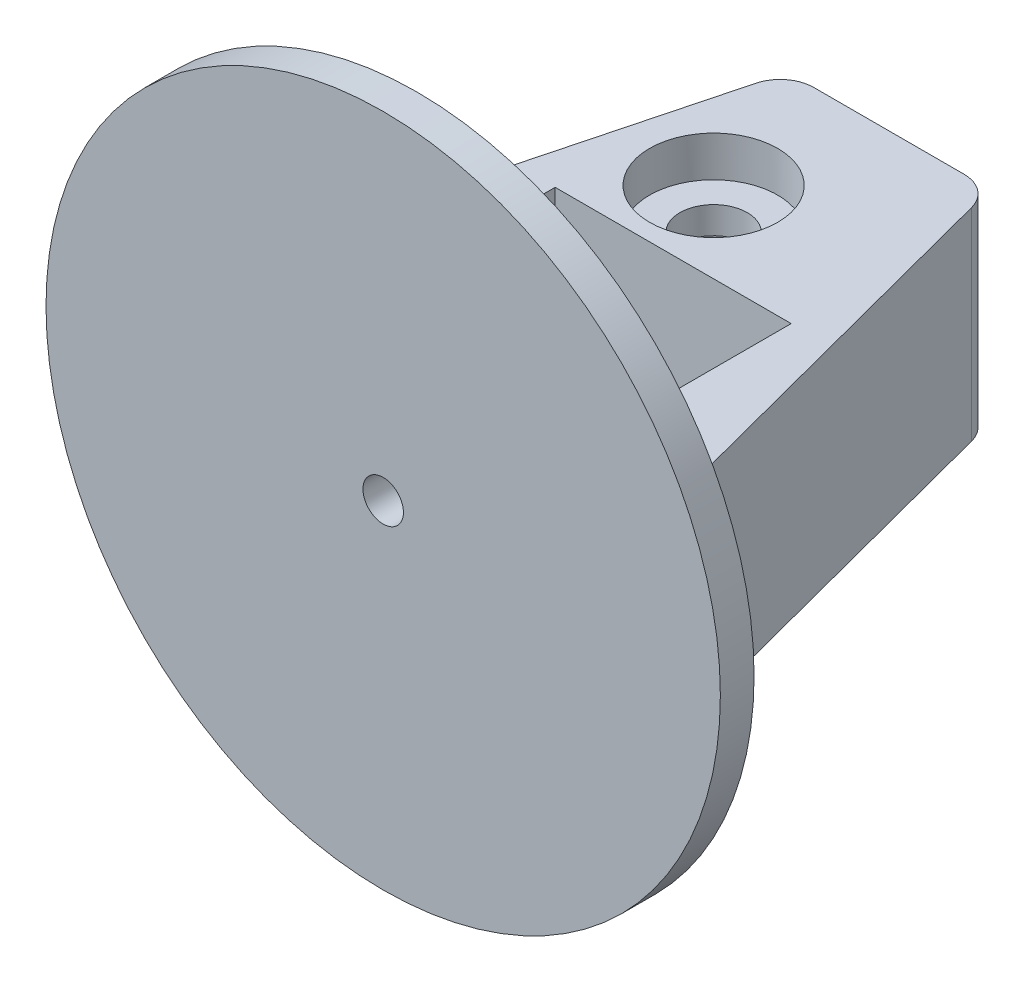
SolidWorks part; units mm, degrees
ref_plane "Front Plane" through (0, 0, 0) normal (0, 0, 1) x (1, 0, 0)
ref_plane "Top Plane" through (0, 0, 0) normal (0, 1, 0) x (1, 0, 0)
ref_plane "Right Plane" through (0, 0, 0) normal (1, 0, 0) x (0, 0, -1)
sketch "Sketch1" plane through (0, 0, 0) normal (0, 1, 0) x (1, 0, 0)
  line L0 (-11.1413, 70) -> (11.1413, 70)
  line L11 (15.9781, 66.2674) -> (33.3421, 0)
  line L12 (33.3421, 0) -> (-33.3421, 0)
  line L13 (-33.3421, 0) -> (-15.9781, 66.2674)
  arc A0 (-11.1413, 70) -> (-15.9781, 66.2674) centre (-11.1413, 65) ccw
  arc A1 (11.1413, 70) -> (15.9781, 66.2674) centre (11.1413, 65) cw
  point P12 (-15, 70)
  point P15 (15, 70)
  dimension "D7" = 5
  dimension "D8" = 5
  dimension "D4" = 30
  dimension "D5" = 70
extrude "Boss-Extrude1" add sketch "Sketch1" along normal blind 40
sketch "Sketch9" plane through (0, 0, 0) normal (0, -1, 0) x (1, 0, 0)
  circle A0 centre (-6, -50) radius 9.5
  dimension "D2" = 19
  dimension "D1" = 50
  dimension "D3" = 6
extrude "Cut-Extrude5" cut sketch "Sketch9" against normal blind 20
sketch "Sketch10" plane through (0, 20, 0) normal (0, -1, 0) x (1, 0, 0)
  circle A0 centre (-6, -50) radius 5
  dimension "D1" = 10
extrude "Cut-Extrude6" cut sketch "Sketch10" against normal through all
sketch "Sketch11" plane through (0, 40, 0) normal (0, 1, 0) x (1, 0, 0)
  circle A0 centre (-6, 50) radius 9.5
  dimension "D1" = 19
extrude "Cut-Extrude7" cut sketch "Sketch11" against normal blind 16
scale "Scale1" [suppressed]
sketch "Sketch13" plane through (0, 0, 0) normal (0, -1, 0) x (1, 0, 0)
  line L0 (0, -57.3655) -> (0, -20.9081) construction
  line L1 (-11, -50) -> (32.9469, -50) construction
  line L2 (9.5, -37.5) -> (-9.5, -37.5)
  line L3 (9.5, -37.5) -> (9.5, -62.5)
  line L4 (9.5, -62.5) -> (-9.5, -62.5)
  line L5 (-9.5, -37.5) -> (-9.5, -62.5)
  circle A0 centre (-6, -50) radius 9.5 construction
  circle A1 centre (-6, -50) radius 9.5 construction
  circle A2 centre (-6, -50) radius 5 construction
  dimension "D1" = 19
  dimension "D2" = 25
extrude "Cut-Extrude8" [suppressed] cut sketch "Sketch13" against normal blind 14
sketch "Sketch14" plane through (0, 40, 0) normal (0, 1, 0) x (1, 0, 0)
  line L1 (-17.5, 18) -> (17.5, 18)
  line L2 (-17.5, 18) -> (-17.5, 38)
  line L3 (-17.5, 38) -> (17.5, 38)
  line L4 (17.5, 18) -> (17.5, 38)
  line L5 (-17.5, 18) -> (17.5, 38) construction
  line L6 (-17.5, 38) -> (17.5, 18) construction
  point P0 (0, 28)
  dimension "D1" = 35
  dimension "D2" = 20
extrude "Cut-Extrude9" cut sketch "Sketch14" against normal through all
sketch "Sketch15" plane through (0, 0, 0) normal (0, 0, 1) x (1, 0, 0)
  line L0 (-33.3421, 20) -> (38.5555, 20) construction
  line L1 (-33.3421, 40) -> (-33.3421, 0) construction
  line L2 (0, 0) -> (0, 49.1924) construction
  circle A0 centre (0, 20) radius 3
  dimension "D1" = 6
  dimension "D2" = 0
extrude "Cut-Extrude10" cut sketch "Sketch15" against normal blind 25
sketch "Sketch16" plane through (0, 0, 0) normal (0, 0, 1) x (1, 0, 0)
  line L0 (0, 0) -> (0, 49.9316) construction
  line L1 (-33.3421, 20) -> (71.4669, 20) construction
  line L2 (-33.3421, 40) -> (-33.3421, 0) construction
  circle A0 centre (0, 20) radius 50
  circle A1 centre (0, 20) radius 3
  dimension "D1" = 100
extrude "Boss-Extrude3" add sketch "Sketch16" along normal blind 5
sketch "Sketch17" plane through (0, 40, 0) normal (0, 1, 0) x (1, 0, 0)
  line L1 (-33.3421, 0) -> (35.8642, 0)
  line L2 (-33.3421, 0) -> (-33.3421, 74.867)
  line L3 (-33.3421, 74.867) -> (35.8642, 74.867)
  line L4 (35.8642, 0) -> (35.8642, 74.867)
extrude "Cut-Extrude11" cut sketch "Sketch17" against normal blind 10
sketch "Sketch18" plane through (0, 0, 0) normal (0, -1, 0) x (1, 0, 0)
  circle A0 centre (-1.3502, -64.85) radius 1.5
  circle A1 centre (-11.3502, -64.85) radius 1.5
  dimension "D1" = 3
  dimension "D2" = 64.85
  dimension "D3" = 10
extrude "Cut-Extrude12" cut sketch "Sketch18" against normal blind 10
sketch "Sketch20" plane through (0, 0, 0) normal (0, -1, 0) x (1, 0, 0)
  circle A0 centre (-11.3502, -14.35) radius 1.5
  circle A1 centre (-1.3502, -14.35) radius 1.5
  dimension "D1" = 3
  dimension "D2" = 3
extrude "Cut-Extrude13" cut sketch "Sketch20" against normal blind 10
